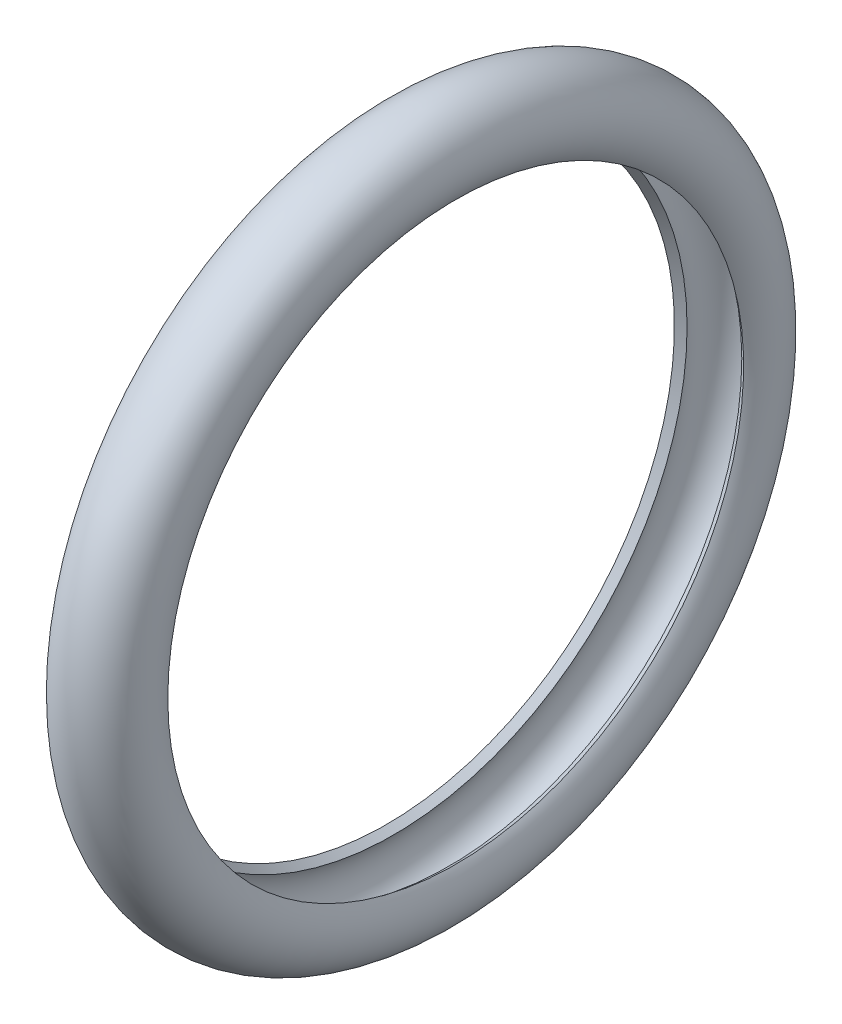
SolidWorks part; units mm, degrees
ref_plane "Front Plane" through (0, 0, 0) normal (0, 0, 1) x (1, 0, 0)
ref_plane "Top Plane" through (0, 0, 0) normal (0, 1, 0) x (1, 0, 0)
ref_plane "Right Plane" through (0, 0, 0) normal (1, 0, 0) x (0, 0, -1)
ref_axis "Axis1" through (-88.99, 0, 0) along (1, 0, 0)
sketch "Sketch1" plane through (0, 0, 0) normal (0, 0, 1) x (1, 0, 0)
  line L0 (-88.99, 0) -> (88.99, 0) construction
  line L1 (0.8922, 10) -> (3.2822, 10) construction
  line L2 (0.8922, 10) -> (0.8922, 7.97) construction
  line L3 (0.8922, 7.97) -> (3.2822, 7.97) construction
  line L4 (3.2822, 10) -> (3.2822, 7.97) construction
  line L5 (1.1297, 7.97) -> (1.33, 8.1196)
  line L6 (3.0447, 7.97) -> (2.8444, 8.1196)
  line L7 (1.1297, 7.97) -> (3.0447, 7.97) construction
  line L8 (0.8922, 9.88) -> (3.2822, 9.88) construction
  arc A0 (3.0447, 7.97) -> (1.1297, 7.97) centre (2.0872, 8.685) ccw
  arc A1 (1.33, 8.1196) -> (2.8444, 8.1196) centre (2.0872, 8.685) cw
  dimension "D1" = 2.39
  dimension "D3" = 20
  dimension "D4" = 0.25
  dimension "D5" = 0.12
  dimension "D6" = 0
  dimension "D2" = 1.91
revolve "Revolve1" add sketch "Sketch1" angle 360 about axis through (-88.99, 0, 0) along (1, 0, 0)
equation "\"DG\" = 20mm"
equation "\"AS\"= 2.39mm"
equation "\"RS\" = 1.91mm"
equation "\"D1@Sketch1\"=\"AS\""
equation "\"D3@Sketch1\"=\"DG\""
equation "\"D2@Sketch1\"=\"RS\""
